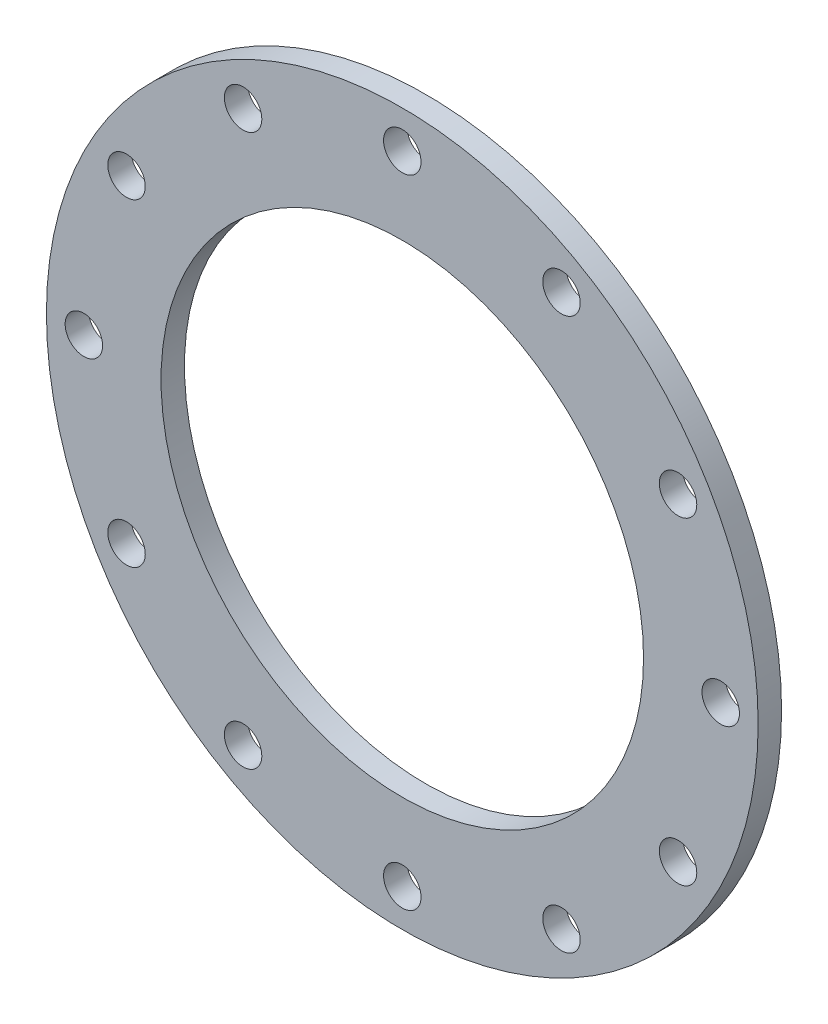
SolidWorks part; units mm, degrees
material "Ductile Iron"
ref_plane "Front Plane" through (0, 0, 0) normal (0, 0, 1) x (1, 0, 0)
ref_plane "Top Plane" through (0, 0, 0) normal (0, 1, 0) x (1, 0, 0)
ref_plane "Right Plane" through (0, 0, 0) normal (1, 0, 0) x (0, 0, -1)
sketch "Profile Sketch" plane through (0, 0, 0) normal (0, 0, 1) x (1, 0, 0)
  circle A0 centre (0, 0) radius 241.3
  circle A1 centre (0, 0) radius 163.576
  circle A2 centre (0, 0) radius 215.9 construction
  circle A3 centre (0, 215.9) radius 12.7 construction
  circle A4 centre (107.95, 186.9749) radius 12.7 construction
  circle A5 centre (186.9749, 107.95) radius 12.7 construction
  circle A6 centre (215.9, 0) radius 12.7 construction
  circle A7 centre (186.9749, -107.95) radius 12.7 construction
  circle A8 centre (107.95, -186.9749) radius 12.7 construction
  circle A9 centre (0, -215.9) radius 12.7 construction
  circle A10 centre (-107.95, -186.9749) radius 12.7 construction
  circle A11 centre (-186.9749, -107.95) radius 12.7 construction
  circle A12 centre (-215.9, 0) radius 12.7 construction
  circle A13 centre (-186.9749, 107.95) radius 12.7 construction
  circle A14 centre (-107.95, 186.9749) radius 12.7 construction
  point P31 (0, 0)
  dimension "D1" = 327.152
  dimension "D2" = 482.6
  dimension "D3" = 431.8
  dimension "D4" = 25.4
  dimension "D5" = 12
extrude "Boss-Extrude1" add sketch "Profile Sketch" along normal mid plane 15.875 contours A0 | A1
hole_wizard "1 (1) Diameter Hole1" positions "3DSketch1" profile "Sketch1" hole size "1" standard "ANSI Inch" end condition through all
sketch3d "3DSketch1"
  point P0 (215.9, 0, 7.9375)
  point P3 (186.9203, -10.5897, 7.9375)
  point P7 (0, 0, 0)
  point P10 (200.3415, -10.1794, 7.9375)
  point P12 (180.0247, 23.8884, 7.9375)
  point P14 (0, 0, 0)
sketch "Sketch1" plane through (215.9, 0, 7.9375) normal (1, 0, 0) x (0, -1, 0)
  line L0 (0, 0) -> (0, 15.875)
  line L1 (0, 15.875) -> (12.7, 15.875)
  line L2 (12.7, 15.875) -> (12.7, 0)
  line L5 (12.7, 0) -> (0, 0)
  line L11 (0, -6.35) -> (0, 107.95) construction
  dimension "Thru Hole Dia." = 25.4
  dimension "Thru Hole Depth" = 15.875
pattern_circular "CirPattern1" count 12 over 360 about axis through (0, 0, 0) along (0, 0, 1) of "1 (1) Diameter Hole1"
equation "\"ID\"= 12.88in'RJSALES"
equation "\"BC\"= 17in'RJSALES"
equation "\"OD\"= 19in'RJSALES"
equation "\"HD\"= 1in'RJSALES"
equation "\"T\"= 0.625in'RJSALES"
equation "\"D1@Profile Sketch\" = \"ID\""
equation "\"D2@Profile Sketch\" = \"OD\""
equation "\"D3@Profile Sketch\" = \"BC\""
equation "\"D4@Profile Sketch\" = \"HD\""
equation "\"D1@Boss-Extrude1\"=\"T\""
